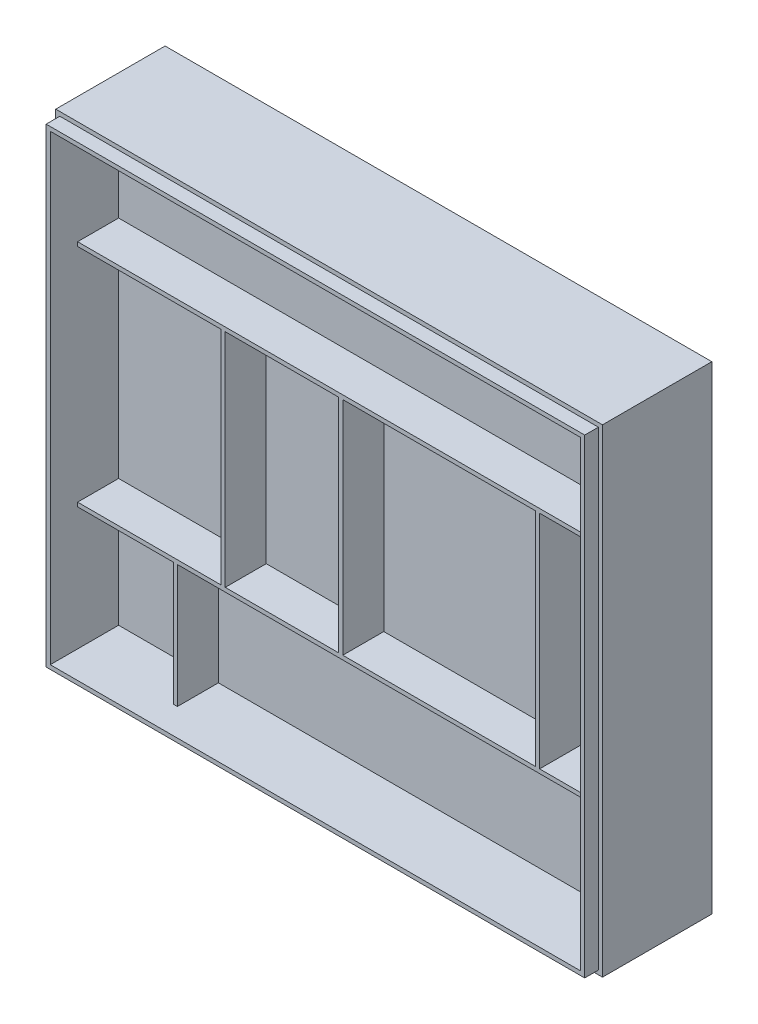
SolidWorks part; units mm, degrees
material "玻璃"
ref_plane "前视基准面" through (0, 0, 0) normal (0, 0, 1) x (1, 0, 0)
ref_plane "上视基准面" through (0, 0, 0) normal (0, 1, 0) x (1, 0, 0)
ref_plane "右视基准面" through (0, 0, 0) normal (1, 0, 0) x (0, 0, -1)
sketch "草图1" plane through (0, 0, 0) normal (0, 0, 1) x (1, 0, 0)
  line L1 (-200, 175) -> (200, 175)
  line L2 (-200, 175) -> (-200, -175)
  line L3 (-200, -175) -> (200, -175)
  line L4 (200, 175) -> (200, -175)
  line L5 (-200, 175) -> (200, -175) construction
  line L6 (-200, -175) -> (200, 175) construction
  point P0 (0, 0)
  dimension "D1" = 400
  dimension "D2" = 350
extrude "凸台-拉伸1" add sketch "草图1" along normal blind 80
sketch "草图2" plane through (0, 0, 80) normal (0, 0, 1) x (1, 0, 0)
  line L0 (200, 175) -> (-200, 175) construction
  line L1 (-197, 172) -> (197, 172)
  line L2 (-197, 172) -> (-197, -172)
  line L3 (-197, -172) -> (197, -172)
  line L4 (197, 172) -> (197, -172)
  line L5 (-197, 172) -> (197, -172) construction
  line L6 (-197, -172) -> (197, 172) construction
  line L7 (-200, 175) -> (-200, -175) construction
  point P0 (0, 0)
  dimension "D1" = 3
  dimension "D2" = 3
extrude "凸台-拉伸2" add sketch "草图2" along normal blind 10
sketch "草图3" plane through (0, 0, 90) normal (0, 0, 1) x (1, 0, 0)
  line L0 (197, 172) -> (-197, 172) construction
  line L1 (-194, 169) -> (194, 169)
  line L2 (-194, 169) -> (-194, -169)
  line L3 (-194, -169) -> (194, -169)
  line L4 (194, 169) -> (194, -169)
  line L5 (-194, 169) -> (194, -169) construction
  line L6 (-194, -169) -> (194, 169) construction
  line L7 (-197, 172) -> (-197, -172) construction
  point P0 (0, 0)
  dimension "D1" = 3
  dimension "D2" = 3
extrude "切除-拉伸1" cut sketch "草图3" against normal blind 50
sketch "草图4" plane through (0, 0, 40) normal (0, 0, 1) x (1, 0, 0)
  line L5 (-194, 169) -> (-194, -169) construction
  line L6 (-194, 89) -> (194, 89)
  line L7 (-194, 89) -> (-194, 86)
  line L8 (-194, 86) -> (194, 86)
  line L9 (194, 89) -> (194, 86)
  line L10 (194, -169) -> (194, 169) construction
  line L11 (194, 169) -> (-194, 169) construction
  line L12 (-194, 169) -> (-194, -169) construction
  line L13 (-194, -76) -> (194, -76)
  line L14 (-194, -76) -> (-194, -79)
  line L15 (-194, -79) -> (194, -79)
  line L16 (194, -76) -> (194, -79)
  line L17 (-194, -169) -> (194, -169) construction
  dimension "D1" = 3
  dimension "D2" = 80
  dimension "D3" = 3
  dimension "D4" = 90
extrude "凸台-拉伸3" add sketch "草图4" along normal blind 30
sketch "草图5" plane through (0, 0, 40) normal (0, 0, 1) x (1, 0, 0)
  line L0 (-194, 86) -> (194, 86) construction
  line L1 (-89, 86) -> (-86, 86)
  line L2 (-89, 86) -> (-89, -76)
  line L3 (-89, -76) -> (-86, -76)
  line L4 (-86, 86) -> (-86, -76)
  line L5 (194, -76) -> (-194, -76) construction
  line L6 (-194, 86) -> (194, 86) construction
  line L7 (-3, 86) -> (0, 86)
  line L8 (-3, 86) -> (-3, -76)
  line L9 (-3, -76) -> (0, -76)
  line L10 (0, 86) -> (0, -76)
  line L11 (194, -76) -> (-194, -76) construction
  line L12 (-194, -79) -> (194, -79) construction
  line L13 (141, 86) -> (144, 86)
  line L14 (141, 86) -> (141, -76)
  line L15 (141, -76) -> (144, -76)
  line L16 (144, 86) -> (144, -76)
  line L17 (-124, -79) -> (-121, -79)
  line L18 (-124, -79) -> (-124, -169)
  line L19 (-124, -169) -> (-121, -169)
  line L20 (-121, -79) -> (-121, -169)
  line L21 (-194, -169) -> (194, -169) construction
  line L22 (-194, 169) -> (-194, -169) construction
  line L23 (194, -76) -> (194, 86) construction
  line L24 (-194, 169) -> (-194, -169) construction
  dimension "D1" = 3
  dimension "D2" = 3
  dimension "D3" = 3
  dimension "D4" = 105
  dimension "D5" = 50
  dimension "D6" = 3
  dimension "D7" = 70
extrude "凸台-拉伸4" add sketch "草图5" along normal blind 30
sketch "草图6" plane through (0, -175, 0) normal (0, -1, 0) x (1, 0, 0)
  line L0 (-200, 0) -> (200, 0) construction
  line L1 (-175, 37) -> (175, 37)
  line L2 (-175, 37) -> (-175, 3)
  line L3 (-175, 3) -> (175, 3)
  line L4 (175, 37) -> (175, 3)
  line L5 (-175, 37) -> (175, 3) construction
  line L6 (-175, 3) -> (175, 37) construction
  point P0 (0, 20)
  dimension "D1" = 350
  dimension "D2" = 20
  dimension "D3" = 3
extrude "切除-拉伸2" cut sketch "草图6" against normal blind 320
chamfer "倒角1" distance 20 angle 45 2 edges at (175, -175, 20) (-175, -175, 20)
